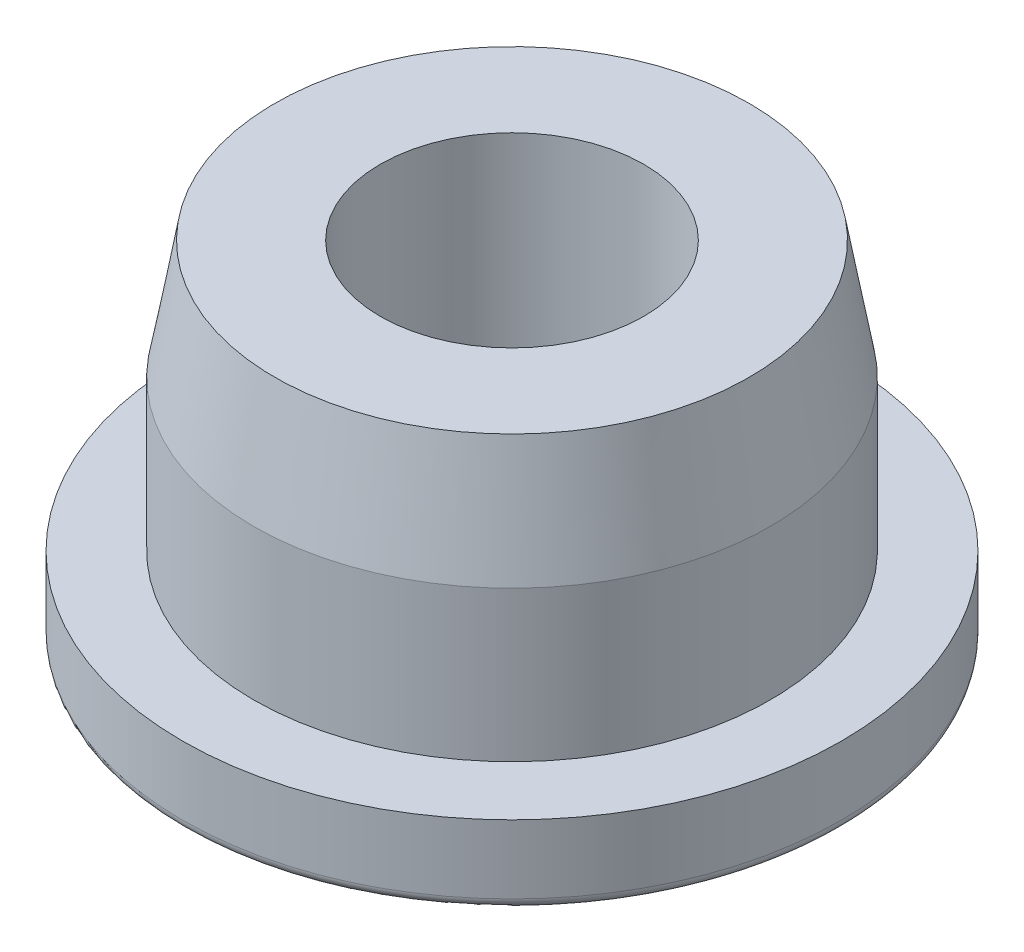
SolidWorks part; units mm, degrees
material "Silicon Rubber"
ref_plane "Front Plane" through (0, 0, 0) normal (0, 0, 1) x (1, 0, 0)
ref_plane "Top Plane" through (0, 0, 0) normal (0, 1, 0) x (1, 0, 0)
ref_plane "Right Plane" through (0, 0, 0) normal (1, 0, 0) x (0, 0, -1)
sketch "Sketch1" plane through (0, 0, 0) normal (1, 0, 0) x (0, 0, -1)
  line L0 (0, 0) -> (0, 13.2863) construction
  line L1 (0, 0) -> (-12.5, 0)
  line L2 (-12.5, 0) -> (-12.5, 3)
  line L3 (-12.5, 3) -> (-9.8, 3)
  line L4 (-9.8, 3) -> (-9.8, 8.7)
  line L5 (-9.8, 8.7) -> (-9, 13.2)
  line L6 (-9, 13.2) -> (-5, 13.2)
  line L7 (-5, 13.2) -> (-5, 2.8)
  line L8 (-5, 2.8) -> (0, 2.8)
  line L9 (0, 2.8) -> (0, 0)
  dimension "D1" = 12.5
  dimension "D2" = 3
  dimension "D3" = 2.7
  dimension "D4" = 13.2
  dimension "D5" = 10.4
  dimension "D6" = 5
  dimension "D7" = 4.5
  dimension "D8" = 4
revolve "Revolve1" add sketch "Sketch1" angle 360 about L0
fillet "Fillet1" radius 0.4 1 edges at (0, 0, -12.5)
